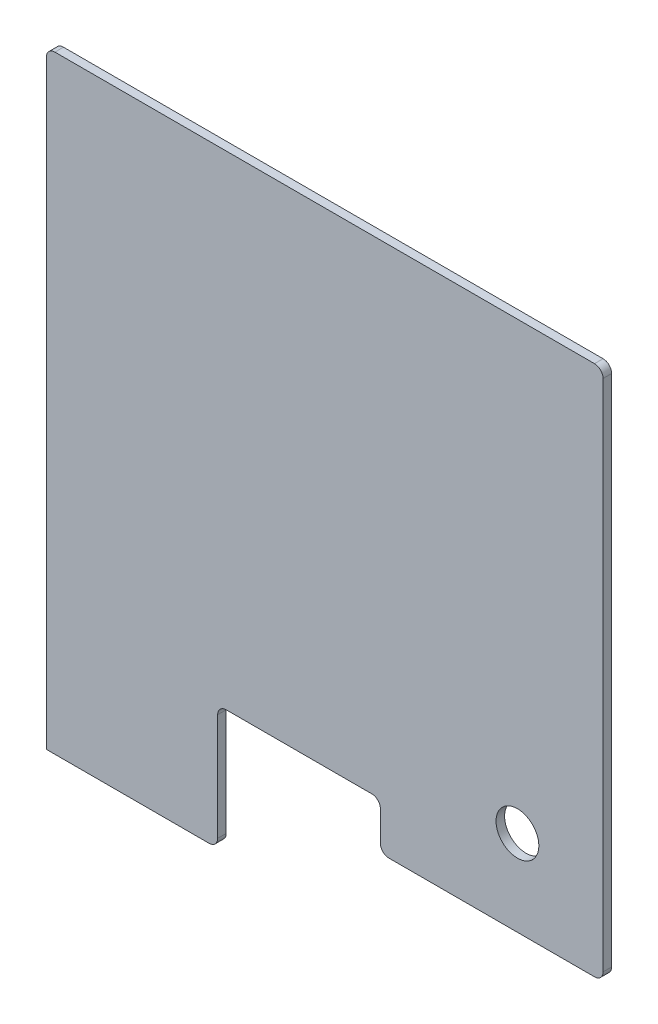
SolidWorks part; units mm, degrees
ref_plane "Front Plane" through (0, 0, 0) normal (0, 0, 1) x (1, 0, 0)
ref_plane "Top Plane" through (0, 0, 0) normal (0, 1, 0) x (1, 0, 0)
ref_plane "Right Plane" through (0, 0, 0) normal (1, 0, 0) x (0, 0, -1)
sketch "Sketch2" plane through (0, 0, 0) normal (0, 0, 1) x (1, 0, 0)
  line L0 (0, 0) -> (-165.1, 0)
  line L1 (-285.75, 34.925) -> (-285.75, -57.15)
  line L2 (-285.75, -57.15) -> (-412.75, -57.15)
  line L3 (-412.75, -57.15) -> (-412.75, 393.7)
  line L4 (-412.75, 393.7) -> (0, 393.7)
  line L5 (0, 393.7) -> (0, 0)
  line L6 (-165.1, 0) -> (-165.1, 34.925)
  line L7 (-165.1, 34.925) -> (-285.75, 34.925)
  circle A0 centre (-63.5, 63.5) radius 15.875
  dimension "D1" = 31.75
  dimension "D2" = 349.25
  dimension "D3" = 330.2
  dimension "D4" = 63.5
  dimension "D5" = 127
  dimension "D6" = 120.65
  dimension "D7" = 120.65
  dimension "D8" = 63.5
  dimension "D9" = 92.075
extrude "Boss-Extrude1" add sketch "Sketch2" along normal blind 6.35
fillet "Fillet1" radius 6.35 7 edges at (-412.75, 393.7, 3.175) (0, 393.7, 3.175) (0, 0, 3.175) (-165.1, 0, 3.175) (-165.1, 34.925, 3.175) (-285.75, 34.925, 3.175) (-285.75, -57.15, 3.175)
sketch "Sketch3" plane through (0, 0, 0) normal (0, 0, -1) x (-1, 0, 0)
  line L0 (-31.75, 0) -> (-31.75, 12.7)
  line L1 (345.44, 44.45) -> (0, 44.45)
  line L2 (381, -83.566) -> (381, 8.89)
  line L3 (292.5229, -215.119) -> (374.8937, -102.2866)
  line L4 (186.69, -95.25) -> (186.69, -145.3879)
  line L5 (0, -31.75) -> (123.19, -31.75)
  line L6 (149.652, 1.2304) -> (155.9906, 1.6107)
  line L7 (190.5, -83.566) -> (190.5, -83.3304)
  line L8 (267.6002, -227.7194) -> (241.8168, -203.1963)
  line L9 (271.3443, -222.5907) -> (267.6002, -227.7194)
  line L10 (271.3443, -222.5907) -> (249.9789, -202.0808)
  line L11 (196.85, -83.566) -> (196.85, -83.3304)
  arc A0 (-31.75, 0) -> (0, -31.75) centre (0, 0) ccw
  arc A1 (0, 44.45) -> (-31.75, 12.7) centre (0, 12.7) ccw
  arc A2 (381, 8.89) -> (345.44, 44.45) centre (345.44, 8.89) ccw
  arc A3 (374.8937, -102.2866) -> (381, -83.566) centre (349.25, -83.566) ccw
  arc A4 (211.8954, -216.9885) -> (292.5229, -215.119) centre (251.493, -185.166) ccw
  arc A5 (186.69, -145.3879) -> (211.8954, -216.9885) centre (300.99, -145.3879) ccw
  arc A6 (186.69, -95.25) -> (123.19, -31.75) centre (123.19, -95.25) ccw
  arc A7 (190.5, -83.3304) -> (149.652, 1.2304) centre (82.55, -83.3304) ccw
  arc A8 (190.5, -83.566) -> (241.8168, -203.1963) centre (355.6, -83.566) ccw
  arc A9 (196.85, -83.566) -> (249.9789, -202.0808) centre (355.6, -83.566) ccw
  arc A10 (196.85, -83.3304) -> (155.9906, 1.6107) centre (82.5812, -85.9995) ccw
  circle A11 centre (355.6, -83.566) radius 1.27
  circle A12 centre (321.0906, 25.4) radius 1.27
  circle A13 centre (0, 0) radius 1.27
sketch "Sketch4" plane through (0, 0, 0) normal (0, 0, -1) x (-1, 0, 0)
  line L0 (-10.6792, -133.35) -> (622.3076, -133.35) construction
  line L1 (431.3524, 373.0476) -> (488.3233, 73.6192)
  line L2 (285.75, 34.925) -> (285.75, -57.15) construction
  line L3 (285.75, -50.8) -> (285.75, -57.15)
  line L4 (349.25, -120.65) -> (425.45, -120.65)
  line L5 (488.95, -57.15) -> (488.95, 16.1726)
  line L6 (285.75, -57.15) -> (412.75, -57.15) construction
  line L7 (412.75, -57.15) -> (412.75, 393.7) construction
  line L8 (0, 6.35) -> (0, 387.35) construction
  line L9 (6.35, 393.7) -> (406.4, 393.7) construction
  line L10 (171.45, 34.925) -> (285.75, 34.925)
  line L12 (285.75, 34.925) -> (285.75, -15.2129)
  line L17 (488.95, 16.1726) -> (488.95, 66.9726)
  line L20 (412.75, 387.35) -> (412.75, -57.15) construction
  line L21 (412.75, -57.15) -> (412.75, 387.35)
  line L22 (406.4, 393.7) -> (6.35, 393.7)
  line L23 (0, 387.35) -> (0, 6.35)
  line L24 (6.35, 0) -> (158.75, 0)
  line L25 (165.1, 6.35) -> (165.1, 28.575)
  line L26 (171.45, 34.925) -> (279.4, 34.925)
  line L27 (285.75, 28.575) -> (285.75, -50.8)
  line L28 (292.1, -57.15) -> (412.75, -57.15)
  line L30 (406.4, 393.7) -> (6.35, 393.7)
  line L31 (0, 387.35) -> (0, 6.35)
  line L32 (6.35, 0) -> (136.525, 0)
  line L34 (171.45, 34.925) -> (279.4, 34.925)
  line L35 (285.75, 28.575) -> (285.75, -50.8)
  line L37 (295.7749, 41.4993) -> (316.2369, -38.4745)
  line L38 (436.6861, 136.3311) -> (463.4441, 31.75) construction
  line L39 (412.0788, 130.0351) -> (438.8368, 25.454) construction
  line L40 (282.3644, 51.003) -> (66.4644, 32.1142)
  circle A0 centre (63.5, 63.5) radius 14.2875
  circle A2 centre (592.954, -332.715) radius 75.057 construction
  circle A3 centre (463.4441, 31.75) radius 25.4
  circle A4 centre (313.1757, -50.8) radius 12.7
  arc A5 (285.75, -57.15) -> (349.25, -120.65) centre (349.25, -57.15) ccw
  arc A6 (425.45, -120.65) -> (488.95, -57.15) centre (425.45, -57.15) ccw
  arc A7 (406.4, 393.7) -> (431.3524, 373.0476) centre (406.4, 368.3) cw
  circle A8 centre (341.63, -88.9) radius 12.7
  arc A9 (282.3644, 51.003) -> (295.7749, 41.4993) centre (283.4713, 38.3513) cw
  arc A10 (165.1, 28.575) -> (136.525, 0) centre (136.525, 28.575) cw
  arc A21 (488.95, 66.9726) -> (488.3233, 73.6192) centre (453.39, 66.9726) ccw
  arc A22 (412.75, 387.35) -> (406.4, 393.7) centre (406.4, 387.35) ccw
  arc A23 (6.35, 393.7) -> (0, 387.35) centre (6.35, 387.35) ccw
  arc A24 (0, 6.35) -> (6.35, 0) centre (6.35, 6.35) ccw
  arc A25 (158.75, 0) -> (165.1, 6.35) centre (158.75, 6.35) ccw
  arc A26 (171.45, 34.925) -> (165.1, 28.575) centre (171.45, 28.575) ccw
  arc A27 (285.75, 28.575) -> (279.4, 34.925) centre (279.4, 28.575) ccw
  arc A28 (285.75, -50.8) -> (292.1, -57.15) centre (292.1, -50.8) ccw
  arc A30 (6.35, 393.7) -> (0, 387.35) centre (6.35, 387.35) ccw
  arc A31 (0, 6.35) -> (6.35, 0) centre (6.35, 6.35) ccw
  arc A33 (171.45, 34.925) -> (165.1, 28.575) centre (171.45, 28.575) ccw
  arc A34 (285.75, 28.575) -> (279.4, 34.925) centre (279.4, 28.575) ccw
  circle A35 centre (436.6861, 136.3311) radius 25.4
  circle A36 centre (358.6147, 177.8) radius 6.35
  dimension "D4" = 150.114
  dimension "D5" = 50.8
  dimension "D6" = 0
  dimension "D7" = 12.7
  dimension "D8" = 76.2
  dimension "D9" = 25.4
  dimension "D10" = 35.56
  dimension "D3" = 196.85
  dimension "D11" = 31.75
  dimension "D12" = 50.1379
  dimension "D13" = 55.88
  dimension "D15" = 25.4
  dimension "D16" = 63.5
  dimension "D20" = 25.4
  dimension "D22" = 139.7
  dimension "D23" = 28.575
  dimension "D18" = 133.35
  dimension "D21" = 27.4257
  dimension "D27" = 12.7
  dimension "D30" = 50.8
  dimension "D35" = 12.7
  dimension "D14" = 304.8
  dimension "D17" = 76.2
  dimension "D19" = 50.8
  dimension "D24" = 38.1
  dimension "D25" = 215.9
  dimension "D26" = 406.4
  dimension "D28" = 82.55
  dimension "D29" = 107.95
  dimension "D31" = 134.62
  dimension "D32" = 10.0249
  dimension "D33" = 5
  dimension "D34" = 6.35
  dimension "D36" = 107.95
  dimension "D37" = 215.9
